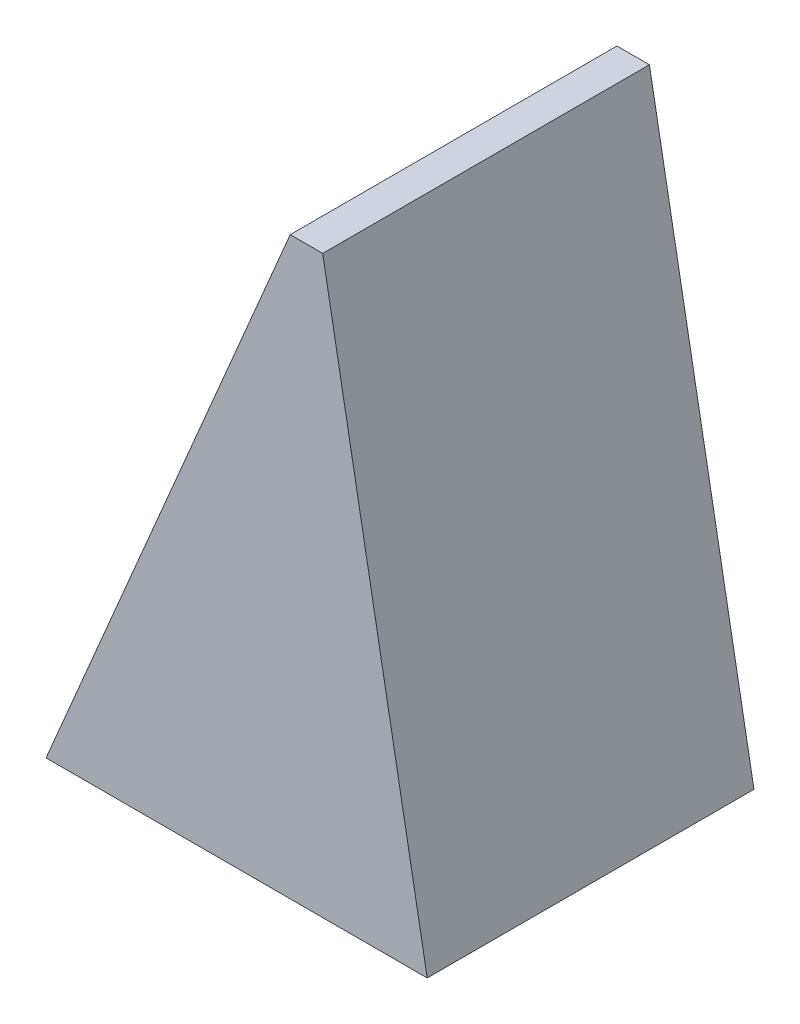
SolidWorks part; units mm, degrees
ref_plane "Front Plane" through (0, 0, 0) normal (0, 0, 1) x (1, 0, 0)
ref_plane "Top Plane" through (0, 0, 0) normal (0, 1, 0) x (1, 0, 0)
ref_plane "Right Plane" through (0, 0, 0) normal (1, 0, 0) x (0, 0, -1)
sketch "Sketch1" plane through (0, 0, 0) normal (0, 0, 1) x (1, 0, 0)
  line L0 (0, 0) -> (0.7, 0)
  line L1 (0.7, 0) -> (0.4902, 1.1547)
  line L2 (0, 0) -> (0.4902, 1.1547)
extrude "Boss-Extrude1" add sketch "Sketch1" along normal blind 0.6
chamfer "Chamfer1" distance 0.1 angle 79.7 1 edges at (0.4902, 1.1547, 0.3)
